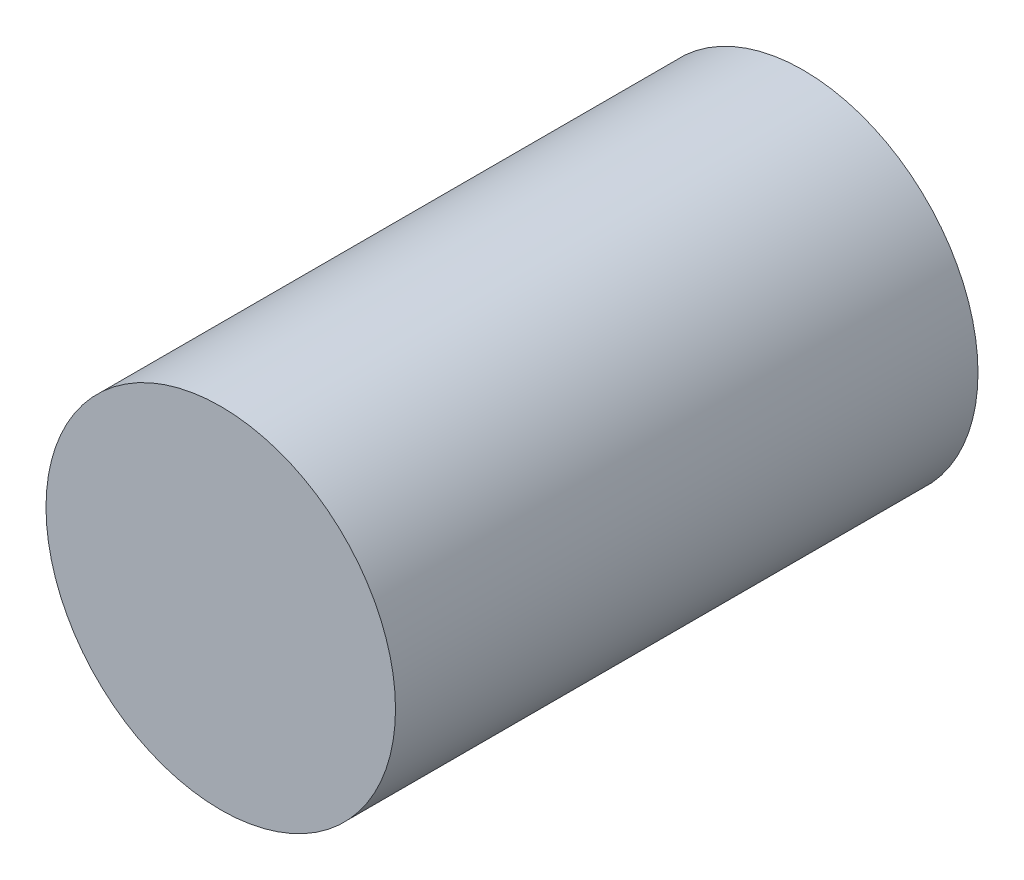
SolidWorks part; units mm, degrees
ref_plane "Front Plane" through (0, 0, 0) normal (0, 0, 1) x (1, 0, 0)
ref_plane "Top Plane" through (0, 0, 0) normal (0, 1, 0) x (1, 0, 0)
ref_plane "Right Plane" through (0, 0, 0) normal (1, 0, 0) x (0, 0, -1)
sketch "Sketch2" plane through (0, 0, 0) normal (0, 0, 1) x (1, 0, 0)
  circle A0 centre (0, 0) radius 1.5
extrude "Boss-Extrude2" add sketch "Sketch2" along normal blind 5
